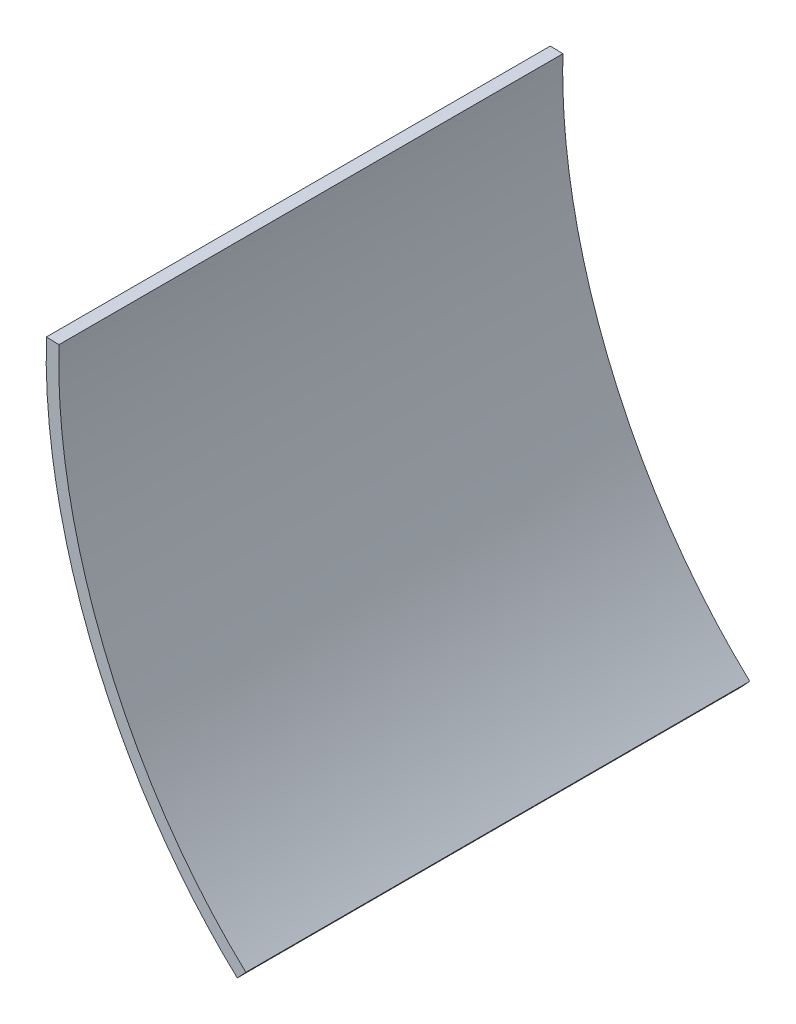
SolidWorks part; units mm, degrees
ref_plane "Front Plane" through (0, 0, 0) normal (0, 0, 1) x (1, 0, 0)
ref_plane "Top Plane" through (0, 0, 0) normal (0, 1, 0) x (1, 0, 0)
ref_plane "Right Plane" through (0, 0, 0) normal (1, 0, 0) x (0, 0, -1)
sketch "Sketch1" plane through (0, 0, 0) normal (0, 0, 1) x (1, 0, 0)
  line L0 (60.0669, -39.5159) -> (62.6058, -39.591)
  line L1 (98.5491, -132.2018) -> (100.2771, -130.3401)
  spline S0 degree 3 poles (100.2771, -130.3401) (76.1, -107.8988) (61.6308, -72.5712) (62.6058, -39.591) knots 0 0 0 0 1 1 1 1
  spline S1 degree 1 poles (98.5491, -132.2018) (60.0669, -39.5159) knots 0 0 1 1 construction
  spline S2 degree 3 poles (98.5491, -132.2018) (95.4371, -129.3132) (89.581, -123.1762) (81.7716, -112.8986) (75.0488, -101.7756) (69.4616, -89.9719) (65.078, -77.6668) (61.9635, -65.0332) (60.483, -54.3802) (60.0034, -45.8626) (60.0043, -41.633) (60.0669, -39.5159) knots 0 0 0 0 0.125 0.25 0.375 0.5 0.625 0.75 0.875 0.9375 1 1 1 1
  dimension "D1" = 2.54
extrude "Boss-Extrude1" add sketch "Sketch1" against normal blind 101.6
